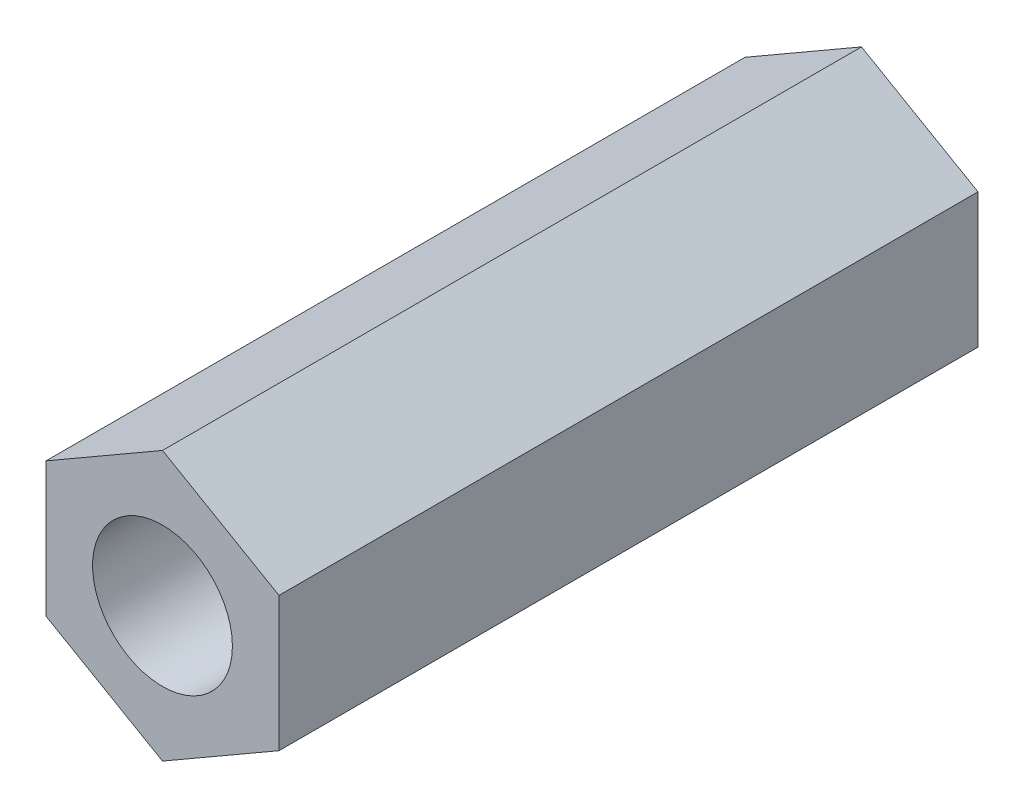
SolidWorks part; units mm, degrees
material "AISI 304"
ref_plane "前视基准面" through (0, 0, 0) normal (0, 0, 1) x (1, 0, 0)
ref_plane "上视基准面" through (0, 0, 0) normal (0, 1, 0) x (1, 0, 0)
ref_plane "右视基准面" through (0, 0, 0) normal (1, 0, 0) x (0, 0, -1)
sketch "草图1" plane through (0, 0, 0) normal (0, 0, 1) x (1, 0, 0)
  line L1 (2.5, 1.4434) -> (0, 2.8868)
  line L2 (0, 2.8868) -> (-2.5, 1.4434)
  line L3 (-2.5, 1.4434) -> (-2.5, -1.4434)
  line L4 (-2.5, -1.4434) -> (0, -2.8868)
  line L5 (0, -2.8868) -> (2.5, -1.4434)
  line L6 (2.5, -1.4434) -> (2.5, 1.4434)
  circle A0 centre (0, 0) radius 2.5 construction
  circle A1 centre (0, 0) radius 1.5
  dimension "D1" = 5
  dimension "D2" = 3
extrude "凸台-拉伸1" add sketch "草图1" along normal blind 15
